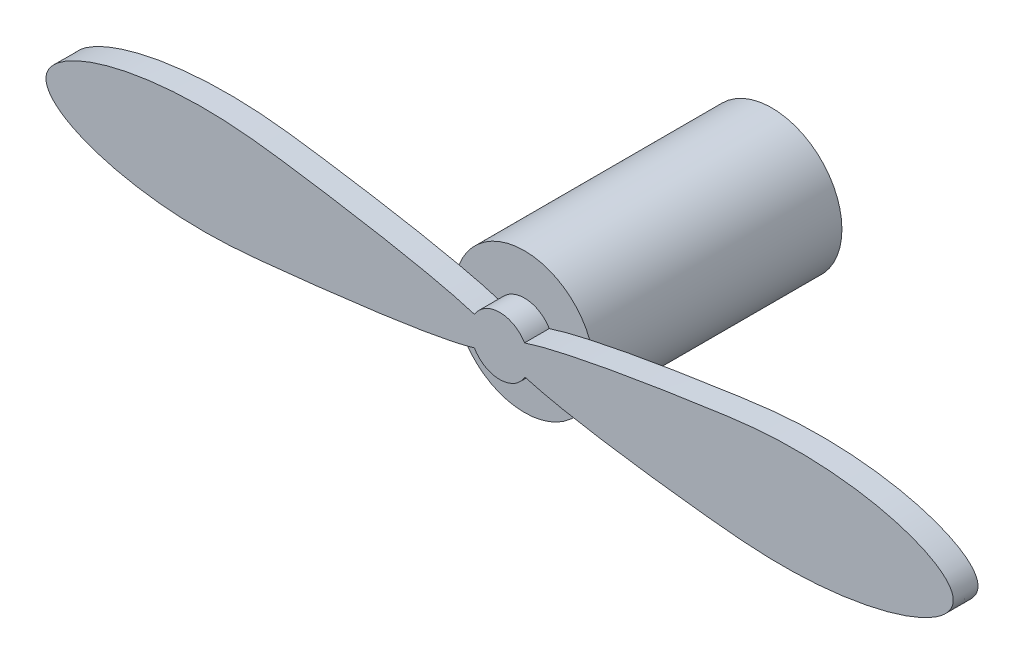
SolidWorks part; units mm, degrees
ref_plane "Front Plane" through (0, 0, 0) normal (0, 0, 1) x (1, 0, 0)
ref_plane "Top Plane" through (0, 0, 0) normal (0, 1, 0) x (1, 0, 0)
ref_plane "Right Plane" through (0, 0, 0) normal (1, 0, 0) x (0, 0, -1)
sketch "Sketch1" plane through (0, 0, 0) normal (0, 0, 1) x (1, 0, 0)
  circle A0 centre (0, 0) radius 4.25
  dimension "D1" = 8.5
extrude "Boss-Extrude1" add sketch "Sketch1" along normal blind 15
sketch "Sketch2" plane through (0, 0, 15) normal (0, 0, 1) x (1, 0, 0)
  line L0 (-27.5, 0.4118) -> (-1.7641, 0.0264) construction
  line L1 (-1.7641, 0.0264) -> (-27.5, 0.4118) construction
  line L2 (1.7641, -0.0264) -> (27.5, -0.4118) construction
  line L3 (-14.6321, 3.2191) -> (-14.6321, -2.7809) construction
  line L4 (0, 4.25) -> (0, 1.7643) construction
  line L5 (1.7641, -0.0264) -> (27.5, -0.4118) construction
  line L6 (0, -1.7643) -> (0, -4.25) construction
  line L7 (0, 0.0128) -> (0, 0) construction
  circle A0 centre (0, 0) radius 4.25 construction
  arc A1 (-1.5337, -0.8721) -> (1.5339, -0.8718) centre (0, 0) ccw
  arc A2 (1.5084, 0.9152) -> (-1.5225, 0.8914) centre (0, 0) ccw
  spline S0 degree 3 poles (-1.5225, 0.8914) (-3.692, 1.5767) (-9.0545, 2.5616) (-21.1324, 4.2374) (-32.4893, 0.4451) (-22.0279, -3.5423) (-10.0012, -2.3139) (-3.7036, -1.519) (-1.5337, -0.8721) knots 0 0 0 0 0.157469 0.200426 0.429573 0.660153 0.703205 0.860096 0.860096 0.860096 0.860096
  spline S1 degree 3 poles (0, 0) (-0.0001, 0.004) (-0.0001, 0.008) (0, 0.012) knots 0 0 0 0 0.000932 0.000932 0.000932 0.000932
  spline S2 degree 3 poles (0, 0) (0.0001, 0.0043) (0.0001, 0.0085) (0, 0.0128) knots 0.929607 0.929607 0.929607 0.929607 0.930618 0.930618 0.930618 0.930618
  spline S3 degree 3 poles (1.5084, 0.9152) (3.674, 1.6153) (9.0413, 2.5554) (21.1264, 4.2424) (32.8276, 0.4482) (21.2245, -3.5542) (9.0522, -2.3282) (3.7053, -1.5183) (1.5339, -0.8718) knots 0.069891 0.069891 0.069891 0.069891 0.227812 0.27082 0.499966 0.730546 0.773598 0.930487 0.930487 0.930487 0.930487
  point P4 (0, 0)
  point P9 (-14.6321, 0.2191)
  dimension "D1" = 55
  dimension "D2" = 6
extrude "Boss-Extrude2" add sketch "Sketch2" along normal blind 1.5
